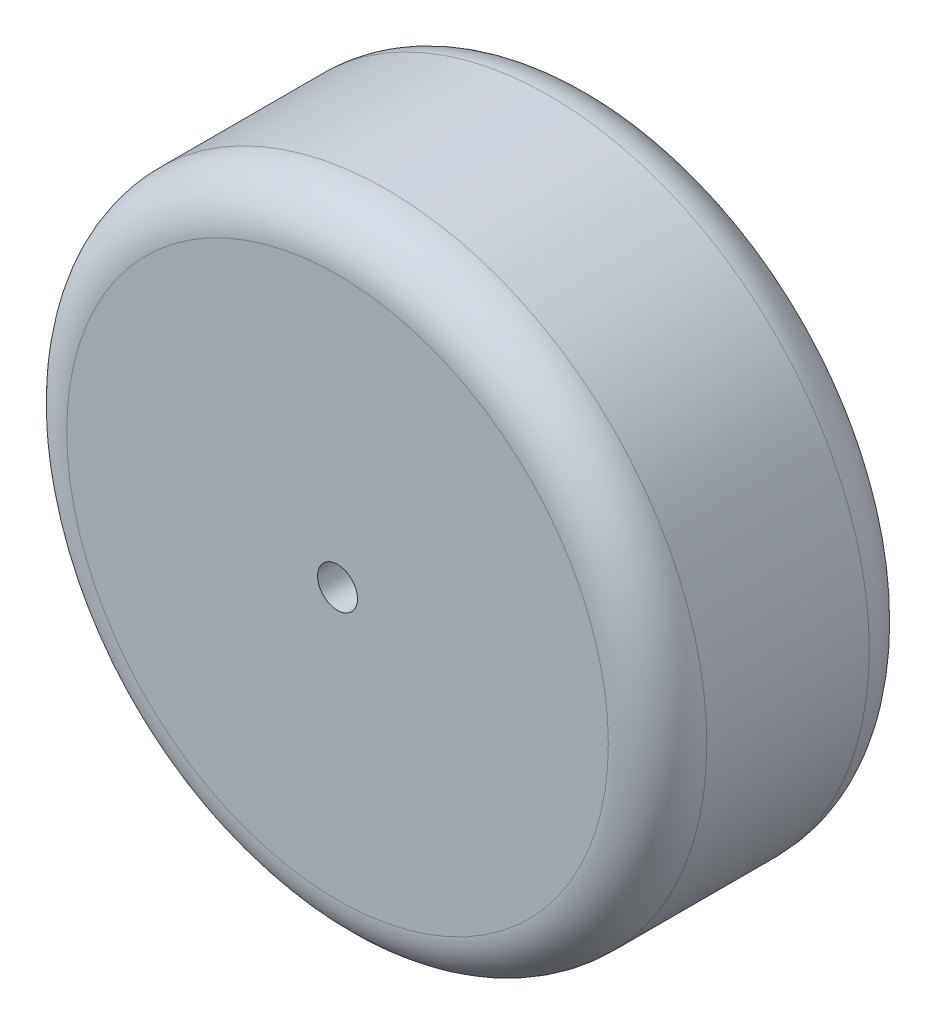
SolidWorks part; units mm, degrees
ref_plane "Plano frontal" through (0, 0, 0) normal (0, 0, 1) x (1, 0, 0)
ref_plane "Plano superior" through (0, 0, 0) normal (0, 1, 0) x (1, 0, 0)
ref_plane "Plano direito" through (0, 0, 0) normal (1, 0, 0) x (0, 0, -1)
sketch "Esboço1" plane through (0, 0, 0) normal (0, 0, 1) x (1, 0, 0)
  circle A0 centre (0, 0) radius 32.5
  dimension "D1" = 65
extrude "Ressalto-extrusão1" add sketch "Esboço1" along normal blind 26.5
sketch "Esboço2" plane through (0, 0, 0) normal (0, 0, -1) x (-1, 0, 0)
  circle A0 centre (0, 0) radius 22.5
  dimension "D1" = 45
extrude "Corte-extrusão1" cut sketch "Esboço2" against normal offset from surface (23.5 mm away) 3 up to face at (32.5, 0, 26.5)
sketch "Esboço3" plane through (0, 0, 23.5) normal (0, 0, -1) x (-1, 0, 0)
  line L1 (6, -3.4641) -> (6, 3.4641)
  line L2 (6, 3.4641) -> (0, 6.9282)
  line L3 (0, 6.9282) -> (-6, 3.4641)
  line L4 (-6, 3.4641) -> (-6, -3.4641)
  line L5 (-6, -3.4641) -> (0, -6.9282)
  line L6 (0, -6.9282) -> (6, -3.4641)
  circle A0 centre (0, 0) radius 9
  circle A1 centre (0, 0) radius 6 construction
  dimension "D1" = 18
  dimension "D2" = 12
extrude "Ressalto-extrusão2" add sketch "Esboço3" along normal blind 15
fillet "Filete1" radius 4 1 edges at (9, 0, 23.5)
sketch "Esboço4" plane through (0, 0, 26.5) normal (0, 0, 1) x (1, 0, 0)
  circle A0 centre (0, 0) radius 2.025
  dimension "D1" = 4.05
extrude "Corte-extrusão2" cut sketch "Esboço4" against normal through all
fillet "Fillet1" radius 5 2 edges at (32.5, 0, 26.5) (32.5, 0, 0)
